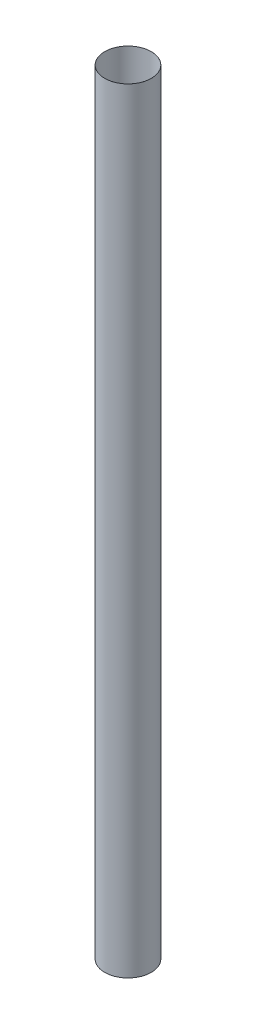
SolidWorks part; units mm, degrees
material "Acrylic (Medium-high impact)"
ref_plane "Front Plane" through (0, 0, 0) normal (0, 0, 1) x (1, 0, 0)
ref_plane "Top Plane" through (0, 0, 0) normal (0, 1, 0) x (1, 0, 0)
ref_plane "Right Plane" through (0, 0, 0) normal (1, 0, 0) x (0, 0, -1)
sketch "Sketch1" plane through (0, 0, 0) normal (0, 1, 0) x (1, 0, 0)
  circle A0 centre (0, 0) radius 38.1
  circle A1 centre (0, 0) radius 38.1254
  dimension "D1" = 76.2
  dimension "D2" = 76.2508
extrude "Boss-Extrude1" add sketch "Sketch1" along normal blind 1270
